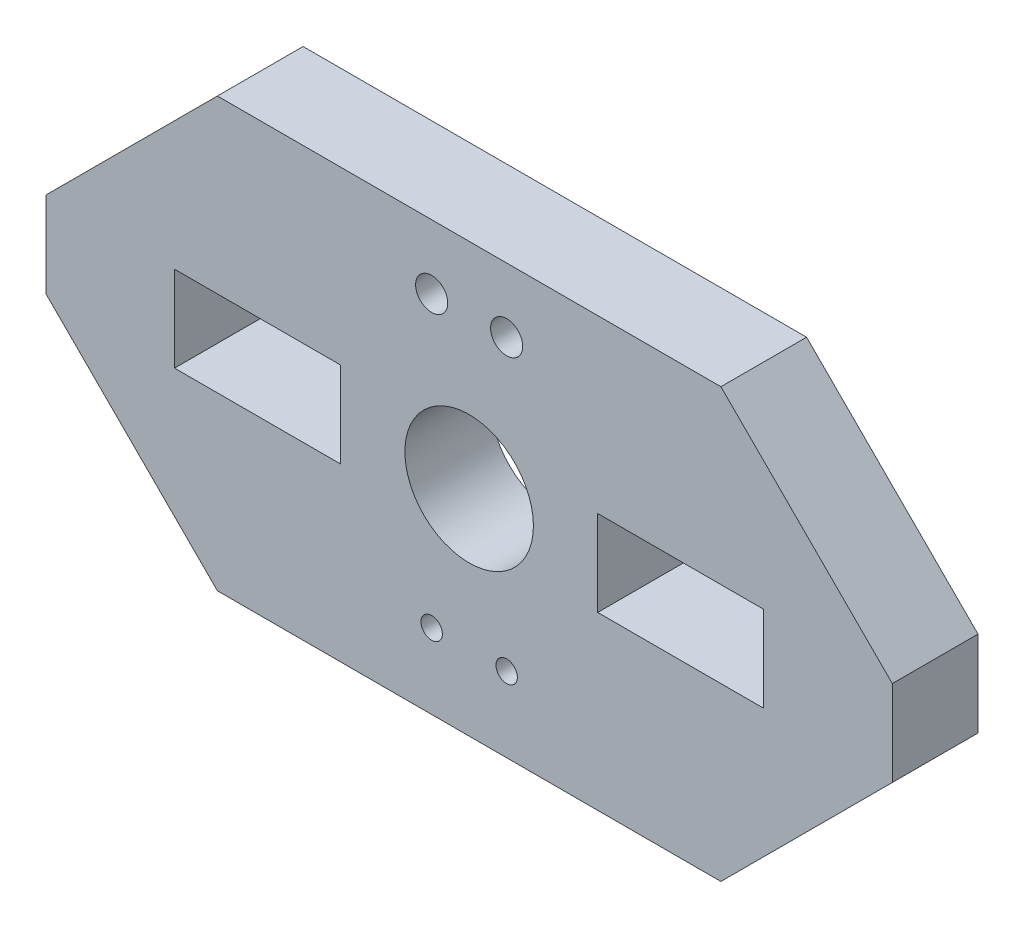
SolidWorks part; units mm, degrees
material "Beech"
ref_plane "Front Plane" through (0, 0, 0) normal (0, 0, 1) x (1, 0, 0)
ref_plane "Top Plane" through (0, 0, 0) normal (0, 1, 0) x (1, 0, 0)
ref_plane "Right Plane" through (0, 0, 0) normal (1, 0, 0) x (0, 0, -1)
sketch "Sketch1" plane through (0, 0, 0) normal (0, 0, 1) x (1, 0, 0)
  line L0 (8, 20) -> (31.5, 20)
  line L1 (39.5, 12) -> (31.5, 20)
  line L2 (39.5, 12) -> (39.5, 8)
  line L3 (31.5, 0) -> (39.5, 8)
  line L4 (31.5, 0) -> (8, 0)
  line L5 (0, 8) -> (0, 12)
  line L6 (8, 0) -> (0, 8)
  line L7 (8, 20) -> (0, 12)
  line L8 (6, 8) -> (6, 12)
  line L9 (6, 12) -> (13.75, 12)
  line L10 (13.75, 12) -> (13.75, 8)
  line L11 (13.75, 8) -> (6, 8)
  line L12 (25.75, 8) -> (25.75, 12)
  line L13 (25.75, 12) -> (33.5, 12)
  line L14 (33.5, 12) -> (33.5, 8)
  line L15 (33.5, 8) -> (25.75, 8)
  circle A0 centre (19.75, 10) radius 3
  circle A1 centre (18, 17) radius 0.75
  circle A2 centre (21.5, 17) radius 0.75
  circle A3 centre (18, 3.5) radius 0.5
  circle A4 centre (21.5, 3.5) radius 0.5
extrude "Boss-Extrude1" add sketch "Sketch1" along normal blind 4
